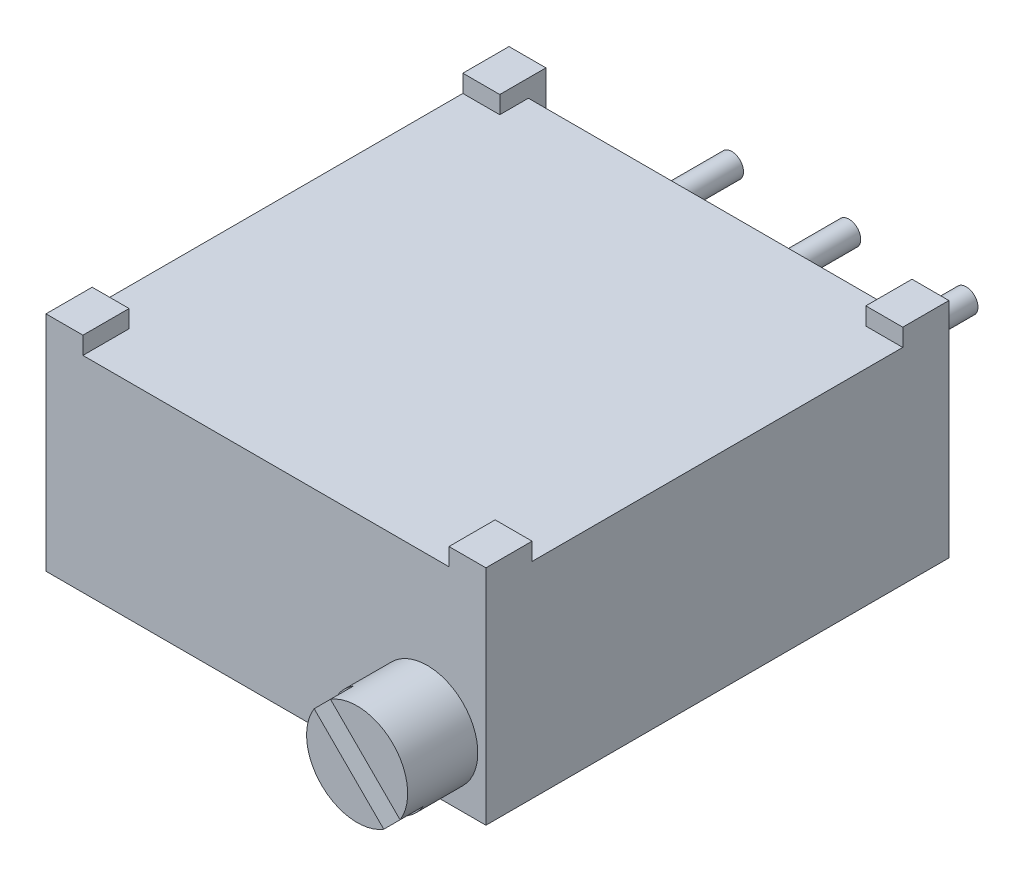
SolidWorks part; units mm, degrees
ref_plane "Plano frontal" through (0, 0, 0) normal (0, 0, 1) x (1, 0, 0)
ref_plane "Plano superior" through (0, 0, 0) normal (0, 1, 0) x (1, 0, 0)
ref_plane "Plano direito" through (0, 0, 0) normal (1, 0, 0) x (0, 0, -1)
sketch "Esboço1" plane through (0, 0, 0) normal (0, 1, 0) x (1, 0, 0)
  line L0 (0, -10.03) -> (0, 0) construction
  line L1 (-4.765, -10.03) -> (4.765, -10.03)
  line L2 (-4.765, -10.03) -> (-4.765, 0)
  line L3 (-4.765, 0) -> (4.765, 0)
  line L4 (4.765, -10.03) -> (4.765, 0)
  dimension "D1" = 9.53
  dimension "D2" = 10.03
extrude "Ressalto-extrusão1" add sketch "Esboço1" along normal mid plane 4.83
sketch "Esboço2" plane through (0, -2.415, 0) normal (0, -1, 0) x (-1, 0, 0)
  line L1 (3.965, 0.62) -> (-3.965, 0.62)
  line L2 (3.965, 0.62) -> (3.965, -0.38)
  line L3 (3.965, -0.38) -> (-3.965, -0.38)
  line L4 (-3.965, 0.62) -> (-3.965, -0.38)
  line L5 (-4.765, 0) -> (4.765, 0) construction
  line L6 (4.765, 0) -> (4.765, -10.03) construction
  line L7 (-4.765, -10.03) -> (-4.765, 0) construction
  dimension "D1" = 0.38
  dimension "D2" = 0.8
  dimension "D3" = 0.8
  dimension "D4" = 1
extrude "Corte-extrusão1" cut sketch "Esboço2" against normal up to next
sketch "Esboço3" plane through (0, 2.415, 0) normal (0, 1, 0) x (1, 0, 0)
  line L0 (3.965, -0.38) -> (-3.965, -0.38)
  line L1 (-3.965, -0.38) -> (-3.965, -1)
  line L3 (-3.965, -1) -> (-4.765, -1)
  line L4 (-4.765, 0) -> (-4.765, -10.03) construction
  line L5 (-4.765, -1) -> (-4.765, -9.03)
  line L7 (-4.765, -9.03) -> (-3.965, -9.03)
  line L8 (-3.965, -9.03) -> (-3.965, -10.03)
  line L9 (-4.765, -10.03) -> (4.765, -10.03) construction
  line L11 (-3.965, -10.03) -> (3.965, -10.03)
  line L12 (3.965, -10.03) -> (3.965, -9.03)
  line L13 (3.965, -9.03) -> (4.765, -9.03)
  line L15 (4.765, -10.03) -> (4.765, 0) construction
  line L16 (4.765, -9.03) -> (4.765, -1)
  line L17 (4.765, -1) -> (3.965, -1)
  line L18 (3.965, -1) -> (3.965, -0.38)
  line L19 (4.765, 0) -> (3.965, 0) construction
  dimension "D1" = 1
  dimension "D2" = 1
extrude "Corte-extrusão2" cut sketch "Esboço3" against normal blind 0.38
sketch "Esboço4" plane through (0, 0, 10.03) normal (0, 0, 1) x (1, 0, 0)
  line L0 (4.765, 2.415) -> (4.765, -2.415) construction
  line L1 (-4.765, -2.415) -> (4.765, -2.415) construction
  circle A0 centre (3.495, -1.145) radius 1.095
  dimension "D3" = 2.19
  dimension "D1" = 1.27
  dimension "D2" = 1.27
extrude "Ressalto-extrusão2" add sketch "Esboço4" along normal blind 1.52
sketch "Esboço5" plane through (0, 0, 11.55) normal (0, 0, 1) x (1, 0, 0)
  line L0 (2.4, -1.145) -> (4.59, -1.145) construction
  line L1 (2.9179, -0.2144) -> (4.4256, -1.7221)
  line L2 (2.5644, -0.5679) -> (4.0721, -2.0756)
  circle A0 centre (3.495, -1.145) radius 1.095 construction
  circle A1 centre (3.495, -1.145) radius 1.095 construction
  arc A2 (4.0721, -2.0756) -> (4.4256, -1.7221) centre (3.495, -1.145) ccw
  arc A3 (2.9179, -0.2144) -> (2.5644, -0.5679) centre (3.495, -1.145) ccw
  point P11 (0, 0)
  dimension "D1" = 0.5
  dimension "D2" = 45
extrude "Corte-extrusão3" cut sketch "Esboço5" against normal blind 0.5
sketch "Esboço6" plane through (0, 0, 0.38) normal (0, 0, -1) x (-1, 0, 0)
  line L0 (-3.965, 2.415) -> (-4.765, 2.415) construction
  line L1 (0, 0.005) -> (0, 0) construction
  line L2 (0, 0.005) -> (-2.54, 0.005) construction
  line L3 (0, 0.005) -> (2.54, 0.005) construction
  circle A0 centre (0, 0.005) radius 0.255
  circle A1 centre (-2.54, 0.005) radius 0.255
  circle A2 centre (2.54, 0.005) radius 0.255
  point P2 (-4.365, 2.415)
  dimension "D2" = 0.51
  dimension "D1" = 2.41
  dimension "D3" = 2.54
  dimension "D4" = 2.54
extrude "Ressalto-extrusão3" add sketch "Esboço6" along normal blind 2.98
